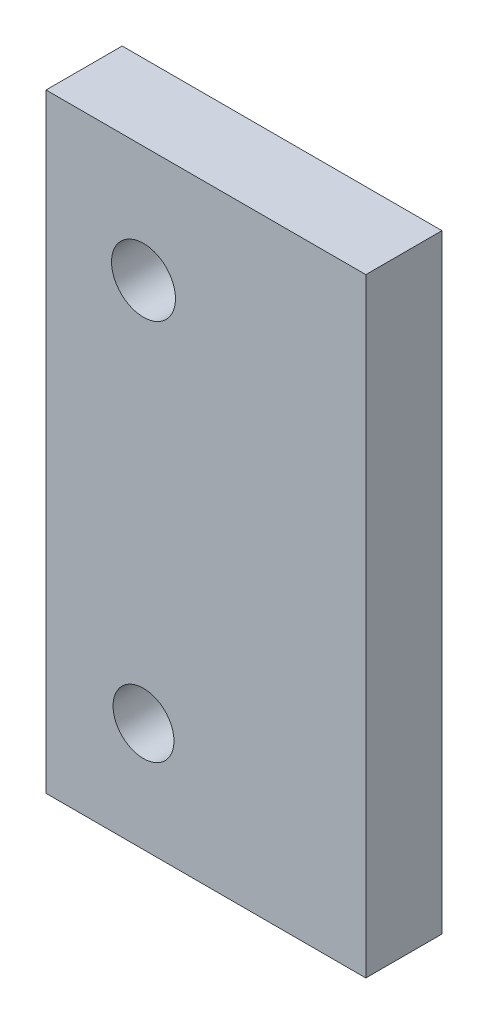
SolidWorks part; units mm, degrees
ref_plane "Front Plane" through (0, 0, 0) normal (0, 0, 1) x (1, 0, 0)
ref_plane "Top Plane" through (0, 0, 0) normal (0, 1, 0) x (1, 0, 0)
ref_plane "Right Plane" through (0, 0, 0) normal (1, 0, 0) x (0, 0, -1)
sketch "Sketch2" plane through (0, 0, 0) normal (0, 0, 1) x (1, 0, 0)
  line L0 (0, 0) -> (0, 20)
  line L1 (0, 20) -> (10.5, 20)
  line L2 (10.5, 20) -> (10.5, 0)
  line L3 (10.5, 0) -> (0, 0)
  dimension "D1" = 10.5
  dimension "D2" = 20
extrude "Boss-Extrude1" add sketch "Sketch2" along normal blind 2.5
sketch "Sketch3" plane through (0, 0, 2.5) normal (0, 0, 1) x (1, 0, 0)
  line L0 (0, 20) -> (0, 0) construction
  circle A0 centre (3.2, 16.1883) radius 1.05
  circle A1 centre (3.2, 3.5883) radius 1
  dimension "D1" = 3.2
  dimension "D2" = 3.2
  dimension "D5" = 2.1
  dimension "D6" = 2
  dimension "D7" = 12.6
extrude "Cut-Extrude1" cut sketch "Sketch3" against normal through all
